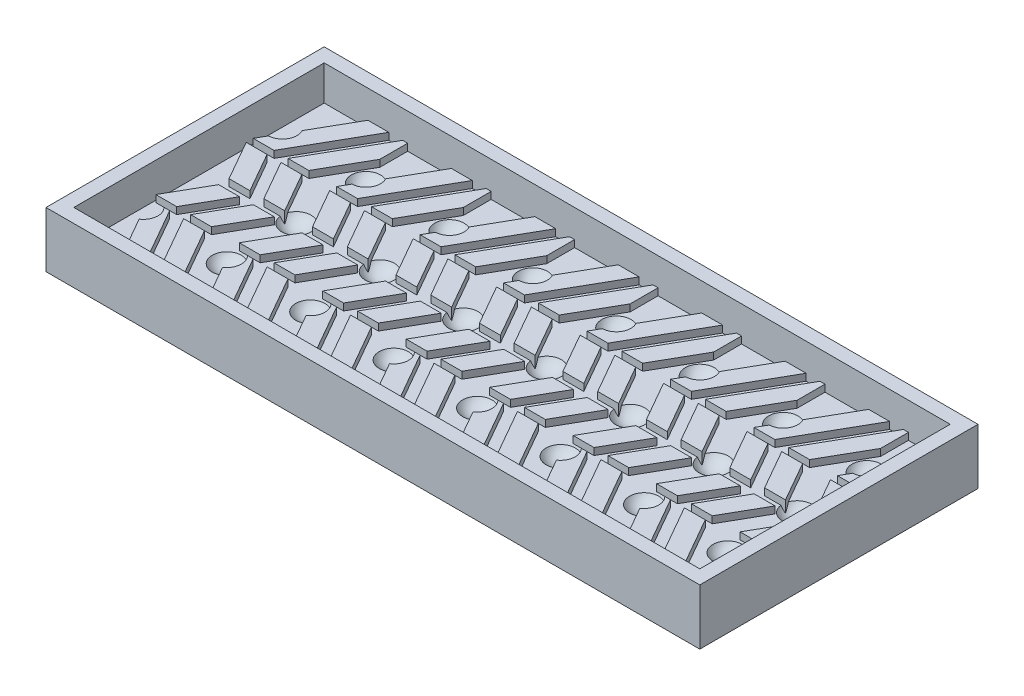
SolidWorks part; units mm, degrees
ref_plane "Front Plane" through (0, 0, 0) normal (0, 0, 1) x (1, 0, 0)
ref_plane "Top Plane" through (0, 0, 0) normal (0, 1, 0) x (1, 0, 0)
ref_plane "Right Plane" through (0, 0, 0) normal (1, 0, 0) x (0, 0, -1)
sketch "Sketch1" plane through (0, 0, 0) normal (0, 1, 0) x (1, 0, 0)
  line L1 (0, 0) -> (132, 0)
  line L2 (0, 0) -> (0, 36)
  line L3 (0, 36) -> (132, 36)
  line L4 (132, 0) -> (132, 36)
  dimension "D1" = 132
  dimension "D2" = 36
extrude "Boss-Extrude1" add sketch "Sketch1" along normal blind 3
ref_plane "Plane1" through (0, 1.3584, 0) normal (0, 1, 0) x (1, 0, 0)
sketch "Sketch4" plane through (0, 1.3584, 0) normal (0, 1, 0) x (1, 0, 0)
  line L0 (121, 36) -> (121, 0)
  line L1 (132, 36) -> (0, 36) construction
  line L2 (0, 0) -> (132, 0) construction
  line L3 (132, 0) -> (132, 36) construction
  circle A0 centre (121, 29) radius 2.5
  dimension "D2" = 5
  dimension "D1" = 11
  dimension "D3" = 7
revolve "Revolve1" add sketch "Sketch4" angle 180 about L0
pattern_linear "LPattern2" count 10 spacing 12 along (-1, 0, 0) count 3 spacing 10 along (0, 0, 1) of "Revolve1"
sketch "Sketch2" plane through (0, 0, 0) normal (0, -1, 0) x (1, 0, 0)
  line L0 (136, -39) -> (128, -25)
  line L1 (132, 0) -> (132, -36) construction
  line L2 (128, -25) -> (132, -18)
  line L3 (132, -36) -> (0, -36) construction
  line L4 (132, -32) -> (132, -18) construction
  line L5 (132, -25) -> (128, -25) construction
  line L6 (132, -18) -> (134, -18) construction
  line L7 (136, 3) -> (128, -11)
  line L8 (128, -11) -> (132, -18)
  line L9 (132, -18) -> (132, -4) construction
  line L10 (132, 0) -> (132, 1.25)
  line L11 (133, 3) -> (125, -11)
  line L12 (125, -11) -> (129, -18)
  line L13 (125, -25) -> (129, -18)
  line L14 (0, 0) -> (0, -36)
  line L15 (0, -36) -> (132, -36)
  line L16 (132, -36) -> (132, 0)
  line L17 (132, 0) -> (0, 0)
  line L18 (0, 0) -> (0, -36)
  line L19 (0, -36) -> (132, -36)
  line L21 (132, 0) -> (0, 0)
  line L22 (133, -39) -> (125, -25)
  line L23 (131.5714, -18.75) -> (128.5714, -18.75)
  line L24 (131.5714, -17.25) -> (128.5714, -17.25)
  line L25 (131, -39) -> (123, -25)
  line L26 (123, -25) -> (127, -18)
  line L27 (131, 3) -> (123, -11)
  line L28 (123, -11) -> (127, -18)
  line L29 (128, 3) -> (120, -11)
  line L30 (120, -11) -> (124, -18)
  line L31 (120, -25) -> (124, -18)
  line L32 (128, -39) -> (120, -25)
  line L33 (126.5714, -18.75) -> (123.5714, -18.75)
  line L34 (126.5714, -17.25) -> (123.5714, -17.25)
  line L35 (127, -32) -> (127, -18) construction
  line L36 (127, -25) -> (123, -25) construction
  line L37 (127, -18) -> (129, -18) construction
  line L38 (127, -18) -> (127, -4) construction
  line L39 (128.2857, -11.5) -> (120.2857, -11.5)
  line L40 (125, -11) -> (128, -11) construction
  line L41 (128.2857, -10.5) -> (120.2857, -10.5)
  line L42 (128.2857, -24.5) -> (120.2857, -24.5)
  line L43 (128.2857, -25.5) -> (120.2857, -25.5)
  line L44 (133, 3) -> (136, 3)
  line L45 (132, -32) -> (132, -37.25) construction
  line L46 (132, -37.25) -> (132, -36)
  line L47 (132, 1.25) -> (132, -4) construction
  line L48 (132, -4) -> (132, -32)
  line L221 (136, -39) -> (131, -39)
  line M281 (132, -36) -> (132, 0)
  dimension "D1" = 4
  dimension "D2" = 4
  dimension "D5" = 3
  dimension "D6" = 0.75
  dimension "D8" = 5
  dimension "D9" = 0.5
  dimension "D3" = 0
  dimension "D4" = 2
  dimension "D7" = 2
extrude "Cut-Extrude1" cut sketch "Sketch2" against normal blind 1 and the other way through all contours L8 L39 L12 L24 | L28 L39 L30 L34 | L42 L26 L33 L31 | L42 L2 L23 L13 | L0 L43 L22 L10 | L25 L43 L32 L19 | L41 L27 L21 L29 | L41 L7 L11 M281
pattern_linear "LPattern1" count 11 spacing 12 along (-1, 0, 0) of "Cut-Extrude1"
sketch "Sketch5" plane through (0, 3, 0) normal (0, 1, 0) x (1, 0, 0)
  line L4 (0, 36) -> (0, 0)
  line L5 (0, 0) -> (132, 0)
  line L6 (132, 0) -> (132, 36)
  line L7 (132, 36) -> (0, 36)
  line L8 (0, 36) -> (0, 0)
  line L9 (0, 0) -> (132, 0)
  line L10 (132, 0) -> (132, 36)
  line L11 (132, 36) -> (0, 36)
  dimension "D1" = 0
extrude "Boss-Extrude2" add sketch "Sketch5" against normal offset from surface (6 mm away) 3 separate body up to face at (57.6397, 0, -21.1487) offset beyond the face yes
combine bodies "Combine2" operation type subtract main body 106 bodies to subtract 103
sketch "Sketch6" plane through (0, -3, 0) normal (0, -1, 0) x (1, 0, 0)
  line L4 (-2, -38) -> (134, -38)
  line L5 (134, -38) -> (134, 2)
  line L6 (134, 2) -> (-2, 2)
  line L7 (-2, 2) -> (-2, -38)
  line L8 (0, -36) -> (132, -36)
  line L9 (132, -36) -> (132, 0)
  line L10 (132, 0) -> (0, 0)
  line L11 (0, 0) -> (0, -36)
  line L12 (0, -36) -> (132, -36) construction
  line L13 (132, -36) -> (132, 0) construction
  line L14 (132, 0) -> (0, 0) construction
  line L15 (0, 0) -> (0, -36) construction
  line M5 (0, -36) -> (132, -36)
  line M6 (132, -36) -> (132, 0)
  line M7 (132, 0) -> (0, 0)
  line M8 (0, 0) -> (0, -36)
  dimension "D1" = 0
  dimension "D2" = 2
extrude "Boss-Extrude3" add sketch "Sketch6" against normal offset from surface (8 mm away) 4 contours L6 L7 L4 L5 M5 M8 M7 M6 up to face at (129.7714, 1, -31) offset beyond the face yes
sketch "Sketch7" plane through (0, 5, 0) normal (0, 1, 0) x (1, 0, 0)
  line L0 (90, 38) -> (90, -2)
  line L1 (134, 38) -> (-2, 38) construction
  line L2 (-2, -2) -> (134, -2) construction
  line L3 (-2, 38) -> (-2, -2) construction
  line L4 (134, -2) -> (134, 38) construction
  line L5 (134, 38) -> (90, 38)
  line L6 (134, -2) -> (134, 38)
  line L7 (90, -2) -> (134, -2)
  dimension "D1" = 92
extrude "Cut-Extrude2" cut sketch "Sketch7" against normal through all both and the other way through all
sketch "Sketch8" plane through (0, -3, 0) normal (0, -1, 0) x (1, 0, 0)
  line L0 (-2, 2) -> (90, 2) construction
  line L1 (90, -38) -> (92, -38)
  line L2 (90, -38) -> (90, 2)
  line L3 (90, 2) -> (92, 2)
  line L4 (92, -38) -> (92, 2)
  dimension "D1" = 2
extrude "Boss-Extrude4" add sketch "Sketch8" against normal up to surface (8 mm away) up to face at (44.5, 5, -18)
